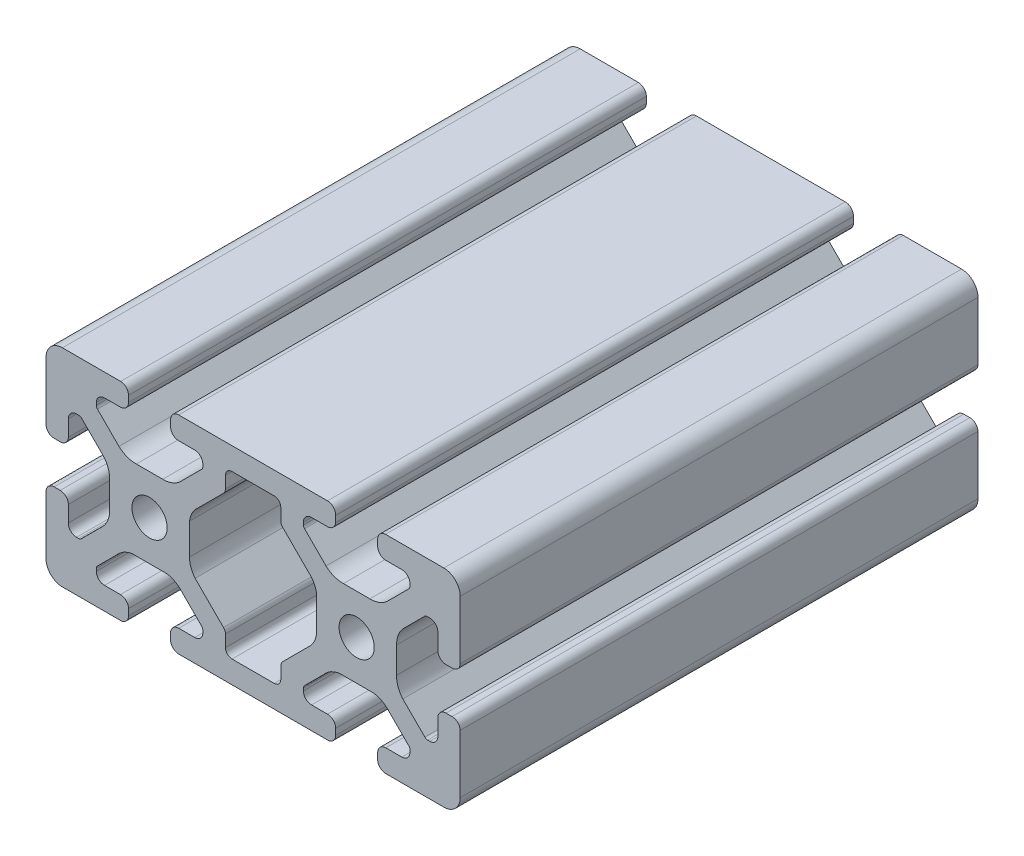
SolidWorks part; units mm, degrees
ref_plane "Front Plane" through (0, 0, 0) normal (0, 0, 1) x (1, 0, 0)
ref_plane "Top Plane" through (0, 0, 0) normal (0, 1, 0) x (1, 0, 0)
ref_plane "Right Plane" through (0, 0, 0) normal (1, 0, 0) x (0, 0, -1)
sketch "Sketch1" plane through (0, 0, 0) normal (0, 0, 1) x (1, 0, 0)
  line L0 (-14.3719, 20) -> (14.3719, 20)
  line L1 (-15.94, 17.1729) -> (-15.94, 18.3529)
  line L2 (-11.285, 15.68) -> (-14.37, 15.68)
  line L3 (-9.715, 13.6545) -> (-9.715, 14.11)
  line L4 (4.0718, 15.68) -> (-4.0718, 15.68)
  line L5 (-5.3418, 14.41) -> (-5.3418, 12.1296)
  line L6 (-5.7137, 11.2316) -> (-10.5988, 6.3465)
  line L7 (-12.2841, 3.2591) -> (-12.2841, -2.725)
  line L8 (5.991, -20) -> (-1.7801, -20)
  line L9 (0, 15.68) -> (0, -15.68) construction
  line L10 (-4.0718, -15.68) -> (4.0718, -15.68)
  line L11 (-5.3418, -12.1296) -> (-5.3418, -14.41)
  line L12 (-11.2012, -5.7441) -> (-5.7137, -11.2316)
  line L13 (-42.275, 0) -> (43.1806, 0) construction
  line L14 (-9.9376, 13.1171) -> (-14.0919, 8.9628)
  line L15 (-17.4506, 7.7) -> (-22.5494, 7.7)
  line L16 (-25.9081, 8.9628) -> (-30.0624, 13.1171)
  line L17 (-30.285, 13.6545) -> (-30.285, 14.11)
  line L18 (-28.715, 15.68) -> (-25.63, 15.68)
  line L19 (-24.06, 17.25) -> (-24.06, 18.4312)
  line L20 (-25.5696, 20) -> (-33, 20)
  line L21 (-33, 20) -> (-36.83, 20)
  line L22 (-40, 16.8406) -> (-40, 13.0106)
  line L23 (-40, 13.0106) -> (-40, 5.5825)
  line L24 (-38.3243, 4.06) -> (-37.1443, 4.06)
  line L25 (-35.68, 5.6264) -> (-35.68, 8.7114)
  line L26 (-34.11, 10.2814) -> (-33.6509, 10.2814)
  line L27 (-33.1135, 10.0588) -> (-29.0111, 5.9564)
  line L28 (-27.7159, 2.571) -> (-27.7159, -2.502)
  line L29 (-28.9155, -5.8608) -> (-33.1719, -10.1172)
  line L30 (-33.7093, -10.3398) -> (-34.111, -10.3398)
  line L31 (-35.68, -8.715) -> (-35.68, -5.63)
  line L32 (-37.25, -4.06) -> (-38.43, -4.06)
  line L33 (-40, -5.5696) -> (-40, -13)
  line L34 (-40, -13) -> (-40, -16.83)
  line L35 (-37.0574, -20) -> (-33.2274, -20)
  line L36 (-33.2274, -20) -> (-25.797, -20)
  line L37 (-24.06, -18.4389) -> (-24.06, -17.25)
  line L38 (-25.63, -15.68) -> (-28.715, -15.68)
  line L39 (-30.285, -14.11) -> (-30.285, -13.6545)
  line L40 (-30.0624, -13.1171) -> (-26.3095, -9.3642)
  line L41 (-23.3415, -7.7) -> (-16.6585, -7.7)
  line L42 (-13.6905, -9.3642) -> (-9.9376, -13.1171)
  line L43 (-9.715, -13.6545) -> (-9.715, -14.11)
  line L44 (-11.285, -15.68) -> (-14.37, -15.68)
  line L45 (-15.94, -17.25) -> (-15.94, -18.43)
  line L46 (-14.37, -20) -> (-5.991, -20)
  line L47 (-5.991, -20) -> (-1.7801, -20)
  line L48 (14.37, -20) -> (5.991, -20)
  line L49 (15.94, -17.25) -> (15.94, -18.43)
  line L50 (11.285, -15.68) -> (14.37, -15.68)
  line L51 (9.715, -13.6545) -> (9.715, -14.11)
  line L52 (13.6905, -9.3642) -> (9.9376, -13.1171)
  line L53 (23.3415, -7.7) -> (16.6585, -7.7)
  line L54 (30.0624, -13.1171) -> (26.3095, -9.3642)
  line L55 (30.285, -14.11) -> (30.285, -13.6545)
  line L56 (25.63, -15.68) -> (28.715, -15.68)
  line L57 (24.06, -18.4389) -> (24.06, -17.25)
  line L58 (33.2274, -20) -> (25.797, -20)
  line L59 (37.0574, -20) -> (33.2274, -20)
  line L60 (40, -13) -> (40, -16.83)
  line L61 (40, -5.5696) -> (40, -13)
  line L62 (37.25, -4.06) -> (38.4312, -4.06)
  line L63 (35.68, -8.715) -> (35.68, -5.63)
  line L64 (33.7093, -10.3398) -> (34.111, -10.3398)
  line L65 (28.9155, -5.8608) -> (33.1719, -10.1172)
  line L66 (27.7159, 2.571) -> (27.7159, -2.502)
  line L67 (33.1135, 10.0588) -> (29.0111, 5.9564)
  line L68 (34.11, 10.2814) -> (33.6509, 10.2814)
  line L69 (35.68, 5.6264) -> (35.68, 8.7114)
  line L70 (38.3243, 4.06) -> (37.1443, 4.06)
  line L71 (40, 13.0106) -> (40, 5.5825)
  line L72 (40, 16.8406) -> (40, 13.0106)
  line L73 (33, 20) -> (36.83, 20)
  line L74 (25.5696, 20) -> (33, 20)
  line L75 (24.06, 17.25) -> (24.06, 18.4312)
  line L76 (28.715, 15.68) -> (25.63, 15.68)
  line L77 (30.285, 13.6545) -> (30.285, 14.11)
  line L78 (25.9081, 8.9628) -> (30.0624, 13.1171)
  line L79 (17.4506, 7.7) -> (22.5494, 7.7)
  line L80 (9.9376, 13.1171) -> (14.0919, 8.9628)
  line L81 (11.2012, -5.7441) -> (5.7137, -11.2316)
  line L82 (5.3418, -12.1296) -> (5.3418, -14.41)
  line L83 (12.2841, 3.2591) -> (12.2841, -2.725)
  line L84 (5.7137, 11.2316) -> (10.5988, 6.3465)
  line L85 (5.3418, 14.41) -> (5.3418, 12.1296)
  line L86 (9.715, 13.6545) -> (9.715, 14.11)
  line L87 (11.285, 15.68) -> (14.37, 15.68)
  line L88 (15.94, 17.1729) -> (15.94, 18.3529)
  line L89 (-20, 24.8708) -> (-20, -18.43) construction
  line L90 (20, 29.4355) -> (20, -23.1087) construction
  line L91 (-3.0962, 16.9038) -> (-43.6857, -23.6857) construction
  line L92 (-36.2671, 16.2671) -> (-2.7875, -17.2125) construction
  arc A0 (-15.94, 18.3529) -> (-14.3719, 20) centre (-14.3719, 18.43) cw
  circle A1 centre (-20, 0) radius 3.4
  arc A2 (-14.37, 15.68) -> (-15.94, 17.1729) centre (-14.3719, 17.25) cw
  arc A3 (-11.285, 15.68) -> (-9.715, 14.11) centre (-11.285, 14.11) cw
  arc A4 (-9.715, 13.6545) -> (-9.9376, 13.1171) centre (-10.475, 13.6545) cw
  arc A5 (-12.2841, -2.725) -> (-11.2012, -5.7441) centre (-7.5341, -2.725) ccw
  arc A6 (-4.0718, 15.68) -> (-5.3418, 14.41) centre (-4.0718, 14.41) ccw
  arc A7 (-5.7137, 11.2316) -> (-5.3418, 12.1296) centre (-6.6118, 12.1296) ccw
  arc A8 (-10.5988, 6.3465) -> (-12.2841, 3.2591) centre (-7.5685, 2.6887) ccw
  arc A9 (-5.3418, -14.41) -> (-4.0718, -15.68) centre (-4.0718, -14.41) ccw
  arc A10 (-5.3418, -12.1296) -> (-5.7137, -11.2316) centre (-6.6118, -12.1296) ccw
  arc A11 (-17.4506, 7.7) -> (-14.0919, 8.9628) centre (-17.3191, 12.4482) ccw
  arc A12 (-25.9081, 8.9628) -> (-22.5494, 7.7) centre (-22.6809, 12.4482) ccw
  arc A13 (-30.285, 13.6545) -> (-30.0624, 13.1171) centre (-29.525, 13.6545) ccw
  arc A14 (-28.715, 15.68) -> (-30.285, 14.11) centre (-28.715, 14.11) ccw
  arc A15 (-25.63, 15.68) -> (-24.06, 17.25) centre (-25.63, 17.25) ccw
  arc A16 (-24.06, 18.4312) -> (-25.5696, 20) centre (-25.63, 18.4312) ccw
  arc A17 (-36.83, 20) -> (-40, 16.8406) centre (-36.83, 16.83) ccw
  arc A18 (-40, 5.5825) -> (-38.3243, 4.06) centre (-38.4306, 5.6264) ccw
  arc A19 (-37.1443, 4.06) -> (-35.68, 5.6264) centre (-37.25, 5.6264) ccw
  arc A20 (-34.11, 10.2814) -> (-35.68, 8.7114) centre (-34.11, 8.7114) ccw
  arc A21 (-33.1135, 10.0588) -> (-33.6509, 10.2814) centre (-33.6509, 9.5214) ccw
  arc A22 (-27.7159, 2.571) -> (-29.0111, 5.9564) centre (-32.4643, 2.6948) ccw
  arc A23 (-28.9155, -5.8608) -> (-27.7159, -2.502) centre (-32.4617, -2.7006) ccw
  arc A24 (-33.7093, -10.3398) -> (-33.1719, -10.1172) centre (-33.7093, -9.5798) ccw
  arc A25 (-35.68, -8.715) -> (-34.111, -10.3398) centre (-34.111, -8.7698) ccw
  arc A26 (-35.68, -5.63) -> (-37.25, -4.06) centre (-37.25, -5.63) ccw
  arc A27 (-38.43, -4.06) -> (-40, -5.5696) centre (-38.4312, -5.63) ccw
  arc A28 (-40, -16.83) -> (-37.0574, -20) centre (-36.83, -16.8382) ccw
  arc A29 (-25.797, -20) -> (-24.06, -18.4389) centre (-25.63, -18.4389) ccw
  arc A30 (-24.06, -17.25) -> (-25.63, -15.68) centre (-25.63, -17.25) ccw
  arc A31 (-30.285, -14.11) -> (-28.715, -15.68) centre (-28.715, -14.11) ccw
  arc A32 (-30.0624, -13.1171) -> (-30.285, -13.6545) centre (-29.525, -13.6545) ccw
  arc A33 (-23.3415, -7.7) -> (-26.3095, -9.3642) centre (-22.6565, -12.4003) ccw
  arc A34 (-13.6905, -9.3642) -> (-16.6585, -7.7) centre (-17.3435, -12.4003) ccw
  arc A35 (-9.715, -13.6545) -> (-9.9376, -13.1171) centre (-10.475, -13.6545) ccw
  arc A36 (-11.285, -15.68) -> (-9.715, -14.11) centre (-11.285, -14.11) ccw
  arc A37 (-14.37, -15.68) -> (-15.94, -17.25) centre (-14.37, -17.25) ccw
  arc A38 (-15.94, -18.43) -> (-14.37, -20) centre (-14.37, -18.43) ccw
  arc A39 (15.94, -18.43) -> (14.37, -20) centre (14.37, -18.43) cw
  arc A40 (14.37, -15.68) -> (15.94, -17.25) centre (14.37, -17.25) cw
  arc A41 (11.285, -15.68) -> (9.715, -14.11) centre (11.285, -14.11) cw
  arc A42 (9.715, -13.6545) -> (9.9376, -13.1171) centre (10.475, -13.6545) cw
  arc A43 (13.6905, -9.3642) -> (16.6585, -7.7) centre (17.3435, -12.4003) cw
  arc A44 (23.3415, -7.7) -> (26.3095, -9.3642) centre (22.6565, -12.4003) cw
  arc A45 (30.0624, -13.1171) -> (30.285, -13.6545) centre (29.525, -13.6545) cw
  arc A46 (30.285, -14.11) -> (28.715, -15.68) centre (28.715, -14.11) cw
  arc A47 (24.06, -17.25) -> (25.63, -15.68) centre (25.63, -17.25) cw
  arc A48 (25.797, -20) -> (24.06, -18.4389) centre (25.63, -18.4389) cw
  arc A49 (40, -16.83) -> (37.0574, -20) centre (36.83, -16.8382) cw
  arc A50 (38.4312, -4.06) -> (40, -5.5696) centre (38.4312, -5.63) cw
  arc A51 (35.68, -5.63) -> (37.25, -4.06) centre (37.25, -5.63) cw
  arc A52 (35.68, -8.715) -> (34.111, -10.3398) centre (34.111, -8.7698) cw
  arc A53 (33.7093, -10.3398) -> (33.1719, -10.1172) centre (33.7093, -9.5798) cw
  arc A54 (28.9155, -5.8608) -> (27.7159, -2.502) centre (32.4617, -2.7006) cw
  arc A55 (27.7159, 2.571) -> (29.0111, 5.9564) centre (32.4643, 2.6948) cw
  arc A56 (33.1135, 10.0588) -> (33.6509, 10.2814) centre (33.6509, 9.5214) cw
  arc A57 (34.11, 10.2814) -> (35.68, 8.7114) centre (34.11, 8.7114) cw
  arc A58 (37.1443, 4.06) -> (35.68, 5.6264) centre (37.25, 5.6264) cw
  arc A59 (40, 5.5825) -> (38.3243, 4.06) centre (38.4306, 5.6264) cw
  arc A60 (36.83, 20) -> (40, 16.8406) centre (36.83, 16.83) cw
  arc A61 (24.06, 18.4312) -> (25.5696, 20) centre (25.63, 18.4312) cw
  arc A62 (25.63, 15.68) -> (24.06, 17.25) centre (25.63, 17.25) cw
  arc A63 (28.715, 15.68) -> (30.285, 14.11) centre (28.715, 14.11) cw
  arc A64 (30.285, 13.6545) -> (30.0624, 13.1171) centre (29.525, 13.6545) cw
  arc A65 (25.9081, 8.9628) -> (22.5494, 7.7) centre (22.6809, 12.4482) cw
  arc A66 (17.4506, 7.7) -> (14.0919, 8.9628) centre (17.3191, 12.4482) cw
  arc A67 (5.3418, -12.1296) -> (5.7137, -11.2316) centre (6.6118, -12.1296) cw
  arc A68 (5.3418, -14.41) -> (4.0718, -15.68) centre (4.0718, -14.41) cw
  arc A69 (10.5988, 6.3465) -> (12.2841, 3.2591) centre (7.5685, 2.6887) cw
  arc A70 (5.7137, 11.2316) -> (5.3418, 12.1296) centre (6.6118, 12.1296) cw
  arc A71 (4.0718, 15.68) -> (5.3418, 14.41) centre (4.0718, 14.41) cw
  arc A72 (12.2841, -2.725) -> (11.2012, -5.7441) centre (7.5341, -2.725) cw
  arc A73 (9.715, 13.6545) -> (9.9376, 13.1171) centre (10.475, 13.6545) ccw
  arc A74 (11.285, 15.68) -> (9.715, 14.11) centre (11.285, 14.11) ccw
  arc A75 (14.37, 15.68) -> (15.94, 17.1729) centre (14.3719, 17.25) ccw
  circle A76 centre (20, 0) radius 3.4
  arc A77 (15.94, 18.3529) -> (14.3719, 20) centre (14.3719, 18.43) ccw
  dimension "D4" = 6.8
  dimension "D1" = 80
  dimension "D2" = 40
  dimension "D3" = 20
  dimension "D5" = 8.12
  dimension "D6" = 4.32
  dimension "D7" = 20.57
  dimension "D8" = 4.32
  dimension "D9" = 12.3
  dimension "D10" = 8.12
  dimension "D11" = 4.32
  dimension "D12" = 4.32
  dimension "D13" = 4.32
extrude "Boss-Extrude1" add sketch "Sketch1" along normal blind 100
